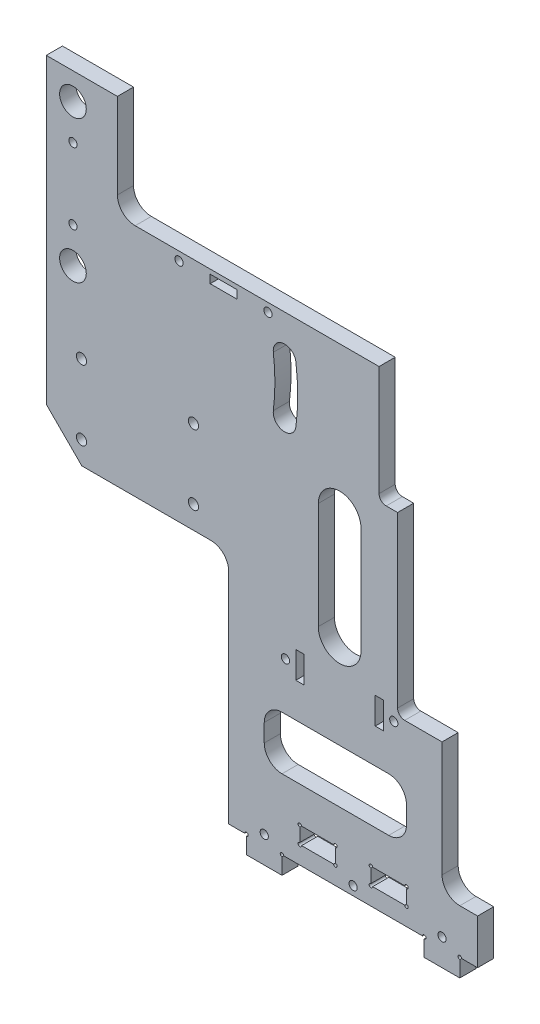
SolidWorks part; units mm, degrees
material "Acrylic (Medium-high impact)"
ref_plane "Front Plane" through (0, 0, 0) normal (0, 0, 1) x (1, 0, 0)
ref_plane "Top Plane" through (0, 0, 0) normal (0, 1, 0) x (1, 0, 0)
ref_plane "Right Plane" through (0, 0, 0) normal (1, 0, 0) x (0, 0, -1)
sketch "Sketch1" plane through (0, 0, 0) normal (0, 0, 1) x (1, 0, 0)
  line L0 (-25.4, 0) -> (25.4, 0)
  line L1 (-25.4, 0) -> (-25.4, -6.35)
  line L2 (-25.4, -6.35) -> (-38.1, -6.35)
  line L3 (-38.1, -6.35) -> (-38.1, 0)
  line L4 (25.4, 0) -> (25.4, -6.35)
  line L5 (25.4, -6.35) -> (38.1, -6.35)
  line L6 (38.1, -6.35) -> (38.1, 0)
  line L7 (-38.1, 0) -> (-44.45, 0)
  line L8 (-109.601, 135.3508) -> (-109.601, 205.2008)
  line L9 (-44.45, 0) -> (-44.45, 135.3508)
  line L11 (38.1, 0) -> (44.45, 0)
  line L12 (82.55, -6.35) -> (107.95, -6.35) construction
  line L13 (44.45, -6.35) -> (69.85, -6.35) construction
  line L14 (44.45, -6.35) -> (44.45, -31.75) construction
  line L15 (44.45, -31.75) -> (69.85, -31.75) construction
  line L16 (69.85, -6.35) -> (69.85, -31.75) construction
  line L17 (44.45, -6.35) -> (69.85, -31.75) construction
  line L18 (44.45, -31.75) -> (69.85, -6.35) construction
  line L19 (82.55, -6.35) -> (82.55, -31.75) construction
  line L20 (82.55, -31.75) -> (107.95, -31.75) construction
  line L21 (107.95, -6.35) -> (107.95, -31.75) construction
  line L22 (82.55, -6.35) -> (107.95, -31.75) construction
  line L23 (82.55, -31.75) -> (107.95, -6.35) construction
  line L24 (-44.45, 135.3508) -> (-109.601, 135.3508)
  line L25 (74.25, 58.002) -> (116.25, 58.002) construction
  line L26 (74.25, 58.002) -> (74.25, 16.002) construction
  line L27 (74.25, 16.002) -> (116.25, 16.002) construction
  line L28 (116.25, 58.002) -> (116.25, 16.002) construction
  line L29 (74.25, 58.002) -> (116.25, 16.002) construction
  line L30 (74.25, 16.002) -> (116.25, 58.002) construction
  line L31 (44.45, 0) -> (44.45, 205.2008)
  line L32 (6.35, 12.3698) -> (19.05, 12.3698)
  line L33 (-19.05, 12.3698) -> (-6.35, 12.3698)
  line L34 (-19.05, 12.3698) -> (-19.05, 6.35)
  line L35 (-19.05, 6.35) -> (-6.35, 6.35)
  line L36 (-6.35, 12.3698) -> (-6.35, 6.35)
  line L37 (-19.05, 12.3698) -> (-6.35, 6.35) construction
  line L38 (-19.05, 6.35) -> (-6.35, 12.3698) construction
  line L39 (6.35, 12.3698) -> (6.35, 6.35)
  line L40 (6.35, 6.35) -> (19.05, 6.35)
  line L41 (19.05, 12.3698) -> (19.05, 6.35)
  line L42 (6.35, 12.3698) -> (19.05, 6.35) construction
  line L43 (6.35, 6.35) -> (19.05, 12.3698) construction
  line L44 (95.25, 37.002) -> (95.25, 170.352) construction
  line L45 (-109.601, 205.2008) -> (44.45, 205.2008)
  line L67 (-12.7, 9.3599) -> (12.7, 9.3599) construction
  circle A0 centre (-100.076, 144.8758) radius 4.7625 construction
  circle A2 centre (-100.076, 195.6758) radius 4.7625 construction
  point P1 (12.7, 9.3599)
  point P9 (57.15, -19.05)
  point P11 (-12.7, 9.3599)
  point P15 (95.25, 87.802)
  point P16 (0, 9.3599)
  point P20 (95.25, -19.05)
  point P25 (95.25, 37.002)
  dimension "D19" = 6.35
  dimension "D20" = 6.0198
  dimension "D21" = 9.525
  dimension "D13" = 9.525
  dimension "D3" = 12.7
  dimension "D4" = 12.7
  dimension "D5" = 50.8
  dimension "D6" = 6.35
  dimension "D7" = 25.4
  dimension "D8" = 25.4
  dimension "D9" = 31.75
  dimension "D10" = 25.4
  dimension "D11" = 25.4
  dimension "D12" = 38.1
  dimension "D14" = 42
  dimension "D15" = 42
  dimension "D16" = 22.352
  dimension "D17" = 195.326
  dimension "D18" = 6.35
  dimension "D22" = 50.8
  dimension "D23" = 9.525
  dimension "D24" = 9.525
  dimension "D25" = 50.8
  dimension "D27" = 12.7
  dimension "D28" = 12.7
  dimension "D29" = 25.4
  dimension "D31" = 107.8738
extrude "Boss-Extrude1" add sketch "Sketch1" along normal blind 5.7658
sketch "Sketch10" plane through (0, 0, 0) normal (0, 0, 1) x (1, 0, 0)
  line L0 (-6.35, 6.35) -> (-6.35, 12.3698) construction
  line L1 (-6.35, 12.3698) -> (-19.05, 12.3698) construction
  line L2 (25.4, 0) -> (25.4, -6.35) construction
  line L3 (-25.4, 0) -> (25.4, 0) construction
  line L4 (-38.1, 0) -> (-38.1, -6.35) construction
  point P0 (-19.05, 12.3698)
  point P1 (-6.35, 12.3698)
  point P3 (-6.35, 6.35)
  point P8 (-19.05, 6.35)
  point P9 (6.35, 12.3698)
  point P11 (19.05, 12.3698)
  point P13 (19.05, 6.35)
  point P15 (6.35, 6.35)
  point P17 (38.1, 0)
  point P19 (25.4, 0)
  point P21 (-25.4, 0)
  point P26 (-38.1, 0)
sketch "Sketch13" plane through (0, 0, 0) normal (0, 0, 1) x (1, 0, 0)
  circle A0 centre (-19.05, 12.3698) radius 0.635
  dimension "D1" = 1.27
extrude "Cut-Extrude2" cut sketch "Sketch13" along normal up to next
pattern_sketch "Sketch-Pattern1" of "Cut-Extrude2" driven by "Sketch10"
chamfer "Chamfer1" distance 50.8 angle 45 1 edges at (44.45, 205.2008, 2.8829)
sketch "Sketch5" plane through (0, 0, 5.7658) normal (0, 0, 1) x (1, 0, 0)
  line L0 (-34.925, 21.0399) -> (-34.925, 0)
  line L1 (-28.575, 21.0399) -> (-28.575, 1.5959)
  line L2 (-34.925, 16.0499) -> (-28.575, 16.0499) construction
  line L3 (-31.75, 16.0499) -> (-31.75, -6.35) construction
  line L5 (-24.765, 0) -> (24.765, 0) construction
  line L6 (-20.9887, 3.175) -> (-22.8217, 6.35)
  line L7 (-22.8217, 6.35) -> (-26.4879, 6.35)
  line L8 (-26.4879, 6.35) -> (-28.321, 3.175)
  line L9 (-28.321, 3.175) -> (-26.4879, 0)
  line L10 (-26.4879, 0) -> (-22.8217, 0)
  line L11 (-22.8217, 0) -> (-20.9887, 3.175)
  line L12 (0, 0) -> (0, 13.7358) construction
  line L13 (-38.1, -6.35) -> (-25.4, -6.35) construction
  circle A0 centre (-24.6548, 3.175) radius 3.175 construction
  point P21 (-38.8452, 3.175)
  point P23 (24.6548, 3.175)
  point P24 (38.8452, 3.175)
  dimension "D1" = 6.35
  dimension "D2" = 6.35
  dimension "D3" = 0.254
hole_wizard "#4 Clearance Hole1" positions "Sketch7" profile "Sketch6" hole size "#4" standard "ANSI Inch"
sketch "Sketch7" plane through (0, 0, 5.7658) normal (0, 0, 1) x (1, 0, 0)
  line L0 (25.4, -6.35) -> (38.1, -6.35) construction
  line L1 (-38.1, -6.35) -> (-25.4, -6.35) construction
  line L2 (-38.8452, 3.175) -> (31.75, 3.175) construction
  line L4 (-31.75, 16.0499) -> (-31.75, -6.35) construction
  point P4 (-31.75, 3.175)
  point P7 (31.75, 3.175)
  point P10 (0, 3.175)
  point P20 (31.75, -6.35)
  point P23 (-31.75, -6.35)
sketch "Sketch6" plane through (-31.75, 3.175, 5.7658) normal (1, 0, 0) x (0, -1, 0)
  line L0 (0, 0) -> (0, 7.2352)
  line L1 (0, 7.2352) -> (1.4732, 6.35)
  line L2 (1.4732, 6.35) -> (1.4732, 0)
  line L5 (1.4732, 0) -> (0, 0)
  line L10 (0, 7.2352) -> (-1.4732, 6.35) construction
  line L11 (0, -6.35) -> (0, 107.95) construction
  dimension "Hole Dia." = 2.9464
  dimension "Hole Depth" = 6.35
  dimension "Drill Angle" = 118
hole_wizard "3/8 (0.375) Diameter Hole1" positions "Sketch23" profile "Sketch22" hole size "3/8" standard "ANSI Inch"
sketch "Sketch23" plane through (0, 0, 5.7658) normal (0, 0, 1) x (1, 0, 0)
  point P0 (-100.076, 144.8758)
  point P4 (-100.076, 195.6758)
sketch "Sketch22" plane through (-100.076, 144.8758, 5.7658) normal (1, 0, 0) x (0, -1, 0)
  line L0 (0, 0) -> (0, 9.2116)
  line L1 (0, 9.2116) -> (4.7625, 6.35)
  line L2 (4.7625, 6.35) -> (4.7625, 0)
  line L5 (4.7625, 0) -> (0, 0)
  line L10 (0, 9.2116) -> (-4.7625, 6.35) construction
  line L11 (0, -6.35) -> (0, 107.95) construction
  dimension "Hole Dia." = 9.525
  dimension "Hole Depth" = 6.35
  dimension "Drill Angle" = 118
sketch "Sketch24" plane through (0, 0, 5.7658) normal (0, 0, 1) x (1, 0, 0)
  line L0 (31.75, 167.1008) -> (31.75, 16.002)
  line L1 (44.45, 154.4008) -> (-6.35, 205.2008) construction
  line L2 (31.75, 16.002) -> (44.45, 16.002)
  line L3 (44.45, 0) -> (44.45, 205.2008) construction
  line L4 (74.25, 16.002) -> (116.25, 16.002) construction
  line L5 (31.75, 167.1008) -> (44.45, 154.4008)
  line L6 (44.45, 154.4008) -> (44.45, 16.002)
  dimension "D1" = 12.7
extrude "Cut-Extrude3" cut sketch "Sketch24" against normal up to next
fillet "Fillet3" radius 6.35 1 edges at (31.75, 16.002, 2.8829)
sketch "Sketch25" plane through (0, 0, 5.7658) normal (0, 0, 1) x (1, 0, 0)
  line L0 (-100.076, 144.8758) -> (101.5302, 119.4758) construction
  line L2 (-100.076, 144.8758) -> (101.5302, 170.2758) construction
  line L4 (-100.076, 195.6758) -> (-100.076, 144.8758) construction
  line L5 (-100.076, 170.2758) -> (59.9088, 170.2758) construction
  arc A0 (-24.4737, 135.3508) -> (-24.4737, 154.4008) centre (-100.076, 144.8758) ccw construction
  arc A1 (-20.4415, 134.8428) -> (-20.4415, 154.9088) centre (-100.076, 144.8758) ccw
  arc A2 (-28.5058, 135.8588) -> (-28.5058, 153.8928) centre (-100.076, 144.8758) ccw
  arc A3 (-28.5058, 135.8588) -> (-20.4415, 134.8428) centre (-24.4737, 135.3508) ccw
  arc A4 (-20.4415, 154.9088) -> (-28.5058, 153.8928) centre (-24.4737, 154.4008) ccw
  arc A10 (13.3275, 159.1633) -> (13.3275, 130.5883) centre (-100.076, 144.8758) cw construction
  arc A11 (17.3596, 130.0803) -> (17.3596, 159.6713) centre (-100.076, 144.8758) ccw
  arc A12 (9.2954, 131.0963) -> (9.2954, 158.6553) centre (-100.076, 144.8758) ccw
  arc A13 (9.2954, 131.0963) -> (17.3596, 130.0803) centre (13.3275, 130.5883) ccw
  arc A14 (17.3596, 159.6713) -> (9.2954, 158.6553) centre (13.3275, 159.1633) ccw
  point P3 (-23.876, 144.8758)
  point P25 (14.224, 144.8758)
  dimension "D1" = 114.3
  dimension "D3" = 4.064
  dimension "D6" = 76.2
  dimension "D7" = 203.2
  dimension "D8" = 50.8
extrude "Cut-Extrude4" cut sketch "Sketch25" against normal up to next
sketch "Sketch26" plane through (0, 0, 5.7658) normal (0, 0, 1) x (1, 0, 0)
  line L0 (-17.526, 61.214) -> (7.874, 61.214) construction
  line L1 (-4.826, 56.4515) -> (-4.826, 65.9765) construction
  line L2 (7.874, 65.9765) -> (7.874, 56.4515)
  line L3 (-20.4851, 65.9765) -> (-17.526, 65.9765)
  line L4 (-20.4851, 65.9765) -> (-20.4851, 56.4515)
  line L5 (-20.4851, 56.4515) -> (-17.526, 56.4515)
  line L6 (-17.526, 65.9765) -> (-17.526, 56.4515)
  line L7 (10.8331, 56.4515) -> (7.874, 56.4515)
  line L8 (10.8331, 65.9765) -> (10.8331, 56.4515)
  line L9 (10.8331, 65.9765) -> (7.874, 65.9765)
  line L11 (-25.4, 0) -> (25.4, 0) construction
  circle A0 centre (-24.1681, 61.214) radius 3.683 construction
  circle A1 centre (14.5161, 61.214) radius 3.683 construction
  point P18 (-4.826, 61.214)
  dimension "D4" = 7.366
  dimension "D1" = 25.4
  dimension "D2" = 2.9591
  dimension "D3" = 9.525
  dimension "D5" = 4.826
  dimension "D6" = 61.214
extrude "Cut-Extrude5" cut sketch "Sketch26" against normal up to next
sketch "Sketch29" plane through (0, 0, 5.7658) normal (0, 0, 1) x (1, 0, 0)
  line L0 (-109.601, 205.2008) -> (44.45, 205.2008) construction
  line L1 (-33.274, 205.2008) -> (31.75, 205.2008)
  line L2 (-33.274, 205.2008) -> (-33.274, 168.3708)
  line L3 (-33.274, 168.3708) -> (31.75, 168.3708)
  line L4 (31.75, 205.2008) -> (31.75, 168.3708)
  line L5 (31.75, 167.1008) -> (31.75, 22.352) construction
  dimension "D1" = 36.83
  dimension "D2" = 65.024
extrude "Cut-Extrude6" cut sketch "Sketch29" against normal up to next
fillet "Fillet5" radius 6.35 1 edges at (-33.274, 168.3708, 2.8829)
sketch "Sketch30" plane through (0, 0, 5.7658) normal (0, 0, 1) x (1, 0, 0)
  line L0 (-109.601, 135.3508) -> (-109.601, 84.5508)
  line L1 (-44.45, 0) -> (-38.735, 0) construction
  line L2 (-109.601, 135.3508) -> (-44.45, 135.3508)
  line L3 (-44.45, 135.3508) -> (-44.45, 84.5508)
  line L4 (-109.601, 84.5508) -> (-44.45, 84.5508)
  line L7 (-101.7905, 120.65) -> (-52.2605, 120.65) construction
  line L8 (-101.7905, 120.65) -> (-101.7905, 63.5) construction
  line L9 (-101.7905, 63.5) -> (-52.2605, 63.5) construction
  line L10 (-52.2605, 120.65) -> (-52.2605, 63.5) construction
  line L11 (-101.7905, 120.65) -> (-52.2605, 63.5) construction
  line L12 (-101.7905, 63.5) -> (-52.2605, 120.65) construction
  point P10 (-77.0255, 92.075)
  point P15 (-77.0255, 135.3508)
  dimension "D1" = 63.5
  dimension "D2" = 57.15
  dimension "D3" = 49.53
  dimension "D4" = 50.8
extrude "Boss-Extrude2" add sketch "Sketch30" against normal up to surface (5.7658 mm away) up to face at (-7.329, 55.4607, 0)
fillet "Fillet6" radius 6.35 1 edges at (-44.45, 84.5508, 2.8829)
sketch "Sketch31" plane through (0, 0, 5.7658) normal (0, 0, 1) x (1, 0, 0)
  line L0 (-17.526, 61.214) -> (7.874, 61.214) construction
  line L1 (-17.526, 56.4515) -> (-17.526, 65.9765) construction
  line L2 (7.874, 65.9765) -> (7.874, 56.4515) construction
  line L3 (-4.826, 61.214) -> (-4.826, 77.0763) construction
  line L4 (-4.826, 77.0763) -> (-4.826, 115.1763) construction
  line L8 (-12.446, 77.0763) -> (-12.446, 115.1763)
  line L9 (2.794, 77.0763) -> (2.794, 115.1763)
  circle A1 centre (-4.826, 77.0763) radius 7.62 construction
  arc A4 (-12.446, 77.0763) -> (2.794, 77.0763) centre (-4.826, 77.0763) ccw
  arc A5 (2.794, 115.1763) -> (-12.446, 115.1763) centre (-4.826, 115.1763) ccw
  point P17 (-4.826, 96.1263)
  dimension "D3" = 15.24
  dimension "D1" = 15.8623
  dimension "D6" = 38.1
sketch "Sketch32" plane through (0, 0, 5.7658) normal (0, 0, 1) x (1, 0, 0)
  line L1 (15.875, 167.5771) -> (25.4, 167.5771)
  line L2 (15.875, 167.5771) -> (15.875, 164.618)
  line L3 (15.875, 164.618) -> (25.4, 164.618)
  line L4 (25.4, 167.5771) -> (25.4, 164.618)
  line L5 (31.75, 167.1008) -> (31.75, 22.352) construction
  line L6 (-26.924, 168.3708) -> (30.48, 168.3708) construction
  dimension "D1" = 9.525
  dimension "D2" = 2.9591
  dimension "D3" = 6.35
  dimension "D4" = 0.7937
extrude "Cut-Extrude9" cut sketch "Sketch32" against normal up to next
hole_wizard "#6 Clearance Hole1" positions "Sketch34" profile "Sketch33" hole size "#6" standard "ANSI Inch"
sketch "Sketch34" plane through (0, 0, 5.7658) normal (0, 0, 1) x (1, 0, 0)
  line L1 (-97.0255, 92.65) -> (-57.0255, 92.65) construction
  line L4 (-101.7905, 120.65) -> (-52.2605, 120.65) construction
  point P0 (-97.0255, 117.65)
  point P2 (-57.0255, 117.65)
  point P4 (-97.0255, 92.65)
  point P6 (-57.0255, 92.65)
  point P23 (-77.0255, 92.65)
  dimension "D1" = 40
  dimension "D2" = 25
  dimension "D3" = 3
sketch "Sketch33" plane through (-97.0255, 117.65, 5.7658) normal (1, 0, 0) x (0, -1, 0)
  line L0 (0, 0) -> (0, 6.9409)
  line L1 (0, 6.9409) -> (1.8288, 5.842)
  line L2 (1.8288, 5.842) -> (1.8288, 0)
  line L5 (1.8288, 0) -> (0, 0)
  line L10 (0, 6.9409) -> (-1.8288, 5.842) construction
  line L11 (0, -6.35) -> (0, 107.95) construction
  dimension "Hole Dia." = 3.6576
  dimension "Hole Depth" = 5.842
  dimension "Drill Angle" = 118
extrude "Cut-Extrude10" cut sketch "Sketch31" against normal up to next
chamfer "Chamfer2" [suppressed] distance 19.05 angle 45
chamfer "Chamfer3" distance 12.7 angle 45 1 edges at (-109.601, 84.5508, 2.8829)
sketch "Sketch35" plane through (0, 0, 5.7658) normal (0, 0, 1) x (1, 0, 0)
  line L0 (31.75, 63.5) -> (15.875, 63.5)
  line L1 (31.75, 167.1008) -> (31.75, 22.352) construction
  line L4 (15.875, 63.5) -> (15.875, 126.5243)
  line L5 (9.2635, 168.3708) -> (31.75, 168.3708)
  line L6 (-26.924, 168.3708) -> (30.48, 168.3708) construction
  line L7 (15.875, 126.5243) -> (9.2635, 126.5243)
  line L8 (31.75, 168.3708) -> (31.75, 63.5)
  line L9 (-25.4, 0) -> (25.4, 0) construction
  line L10 (9.2635, 126.5243) -> (9.2635, 168.3708)
  arc A0 (9.2954, 131.0963) -> (17.3596, 130.0803) centre (13.3275, 130.5883) ccw construction
  dimension "D1" = 63.5
  dimension "D3" = 15.875
extrude "Cut-Extrude11" cut sketch "Sketch35" against normal up to next
sketch "Sketch36" plane through (0, 0, 5.7658) normal (0, 0, 1) x (1, 0, 0)
  line L0 (-26.924, 168.3708) -> (-84.201, 168.3708)
  line L1 (-84.201, 168.3708) -> (-84.201, 205.2008)
  line L2 (-109.601, 205.2008) -> (44.45, 205.2008) construction
  line L3 (-84.201, 205.2008) -> (-26.924, 205.2008)
  line L4 (-26.924, 205.2008) -> (-26.924, 168.3708)
  line L5 (-109.601, 195.6758) -> (-104.8385, 195.6758) construction
  line L6 (-109.601, 135.3508) -> (-109.601, 205.2008) construction
  circle A0 centre (-100.076, 195.6758) radius 4.7625 construction
  dimension "D1" = 25.4
extrude "Cut-Extrude12" cut sketch "Sketch36" against normal up to next
fillet "Fillet7" radius 2.54 2 edges at (9.2635, 126.5243, 2.8829) (15.875, 63.5, 2.8829)
fillet "Fillet8" radius 6.35 1 edges at (-84.201, 168.3708, 2.8829)
sketch "Sketch37" plane through (0, 0, 5.7658) normal (0, 0, 1) x (1, 0, 0)
  line L1 (-51.0615, 166.7833) -> (-41.5365, 166.7833)
  line L2 (-51.0615, 166.7833) -> (-51.0615, 163.8242)
  line L3 (-51.0615, 163.8242) -> (-41.5365, 163.8242)
  line L4 (-41.5365, 166.7833) -> (-41.5365, 163.8242)
  line L5 (-77.851, 168.3708) -> (9.2635, 168.3708) construction
  line L6 (9.2635, 168.3708) -> (9.2635, 129.0643) construction
  dimension "D1" = 9.525
  dimension "D2" = 2.9591
  dimension "D3" = 1.5875
  dimension "D4" = 50.8
extrude "Cut-Extrude13" cut sketch "Sketch37" against normal up to next
hole_wizard "#4 Clearance Hole2" positions "Sketch28" profile "Sketch27" hole size "#4" standard "ANSI Inch" end condition up to next
sketch "Sketch28" plane through (0, 0, 5.7658) normal (0, 0, 1) x (1, 0, 0)
  line L1 (-100.076, 182.9758) -> (-100.076, 157.5758) construction
  line L15 (-77.851, 168.3708) -> (9.2635, 168.3708) construction
  line L16 (-62.174, 165.3038) -> (-30.424, 165.3038) construction
  line L18 (-46.299, 166.7833) -> (-46.299, 163.8242) construction
  line L19 (-41.5365, 166.7833) -> (-51.0615, 166.7833) construction
  line L20 (-51.0615, 163.8242) -> (-41.5365, 163.8242) construction
  point P0 (-24.1681, 61.214)
  point P3 (14.5161, 61.214)
  point P6 (20.6375, 117.5708)
  point P8 (-100.076, 182.9758)
  point P10 (-100.076, 157.5758)
  point P73 (-62.174, 165.3038)
  point P75 (-30.424, 165.3038)
  point P90 (-46.299, 165.3038)
  dimension "D3" = 50.8
  dimension "D4" = 31.75
  dimension "D1" = 12.7
  dimension "D2" = 12.7
sketch "Sketch27" plane through (-24.1681, 61.214, 5.7658) normal (1, 0, 0) x (0, -1, 0)
  line L0 (0, 0) -> (0, 5.7658)
  line L1 (0, 5.7658) -> (1.4732, 5.7658)
  line L2 (1.4732, 5.7658) -> (1.4732, 0)
  line L5 (1.4732, 0) -> (0, 0)
  line L11 (0, -6.35) -> (0, 107.95) construction
  dimension "Thru Hole Dia." = 2.9464
  dimension "Thru Hole Depth" = 5.7658
sketch "Sketch38" plane through (0, 0, 5.7658) normal (0, 0, 1) x (1, 0, 0)
  line L0 (-44.45, 34.5948) -> (31.75, 34.5948) construction
  line L1 (-31.75, 44.1198) -> (19.05, 44.1198)
  line L2 (-31.75, 44.1198) -> (-31.75, 25.0698)
  line L3 (-31.75, 25.0698) -> (19.05, 25.0698)
  line L4 (19.05, 44.1198) -> (19.05, 25.0698)
  line L5 (-31.75, 44.1198) -> (19.05, 25.0698) construction
  line L6 (-31.75, 25.0698) -> (19.05, 44.1198) construction
  line L7 (-44.45, 78.2008) -> (-44.45, 0) construction
  line L8 (31.75, 63.5) -> (31.75, 22.352) construction
  line L9 (18.415, 12.3698) -> (6.985, 12.3698) construction
  point P0 (-6.35, 34.5948)
  dimension "D1" = 50.8
  dimension "D2" = 19.05
  dimension "D3" = 31.75
extrude "Cut-Extrude14" cut sketch "Sketch38" against normal through all
fillet "Fillet9" radius 6.35 4 edges at (19.05, 25.0698, 2.8829) (19.05, 44.1198, 2.8829) (-31.75, 25.0698, 2.8829) (-31.75, 44.1198, 2.8829)
